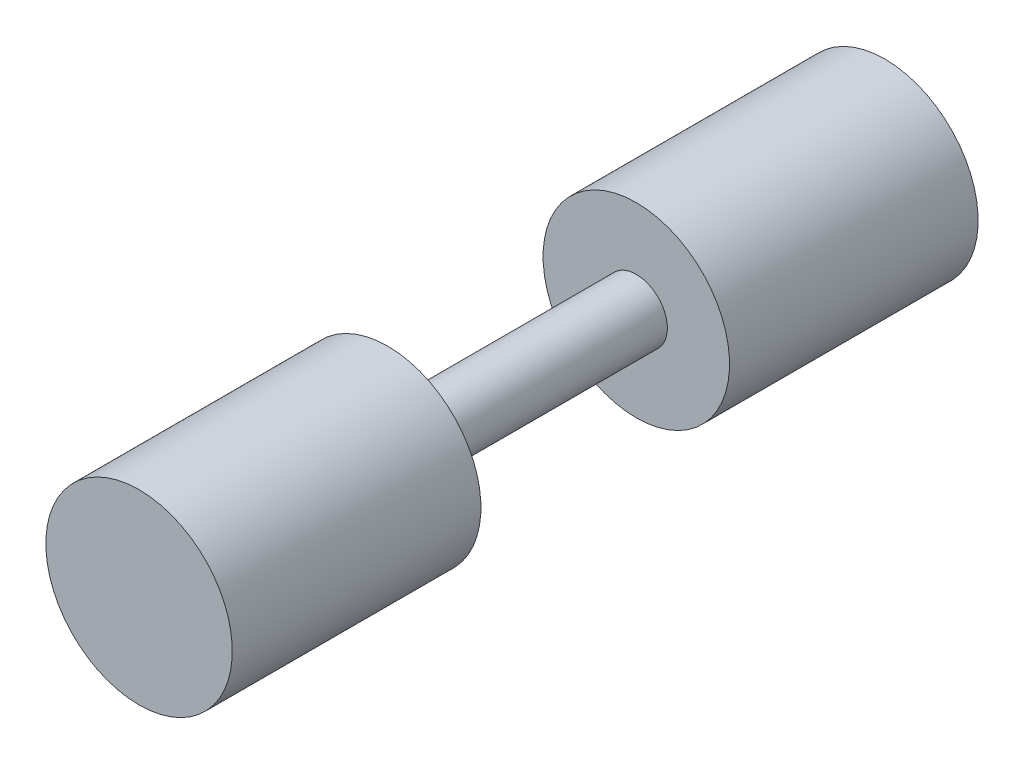
SolidWorks part; units mm, degrees
material "6061 Alloy"
ref_plane "Front Plane" through (0, 0, 0) normal (0, 0, 1) x (1, 0, 0)
ref_plane "Top Plane" through (0, 0, 0) normal (0, 1, 0) x (1, 0, 0)
ref_plane "Right Plane" through (0, 0, 0) normal (1, 0, 0) x (0, 0, -1)
sketch "Sketch1" plane through (0, 0, 0) normal (1, 0, 0) x (0, 0, -1)
  line L0 (76.2, 0) -> (-76.2, 0)
  line L1 (-76.2, 0) -> (-76.2, 19.05)
  line L2 (-76.2, 19.05) -> (-25.4, 19.05)
  line L3 (-25.4, 19.05) -> (-25.4, 6.35)
  line L4 (-25.4, 6.35) -> (25.4, 6.35)
  line L5 (25.4, 6.35) -> (25.4, 19.05)
  line L6 (25.4, 19.05) -> (76.2, 19.05)
  line L7 (76.2, 19.05) -> (76.2, 0)
  point P4 (0, 0)
  point P11 (-26.9875, 19.8438)
  point P12 (-24.0393, 19.05)
  dimension "D1" = 50.8
  dimension "D2" = 19.05
  dimension "D3" = 6.35
  dimension "D4" = 152.4
revolve "Revolve1" add sketch "Sketch1" angle 360 about L0
